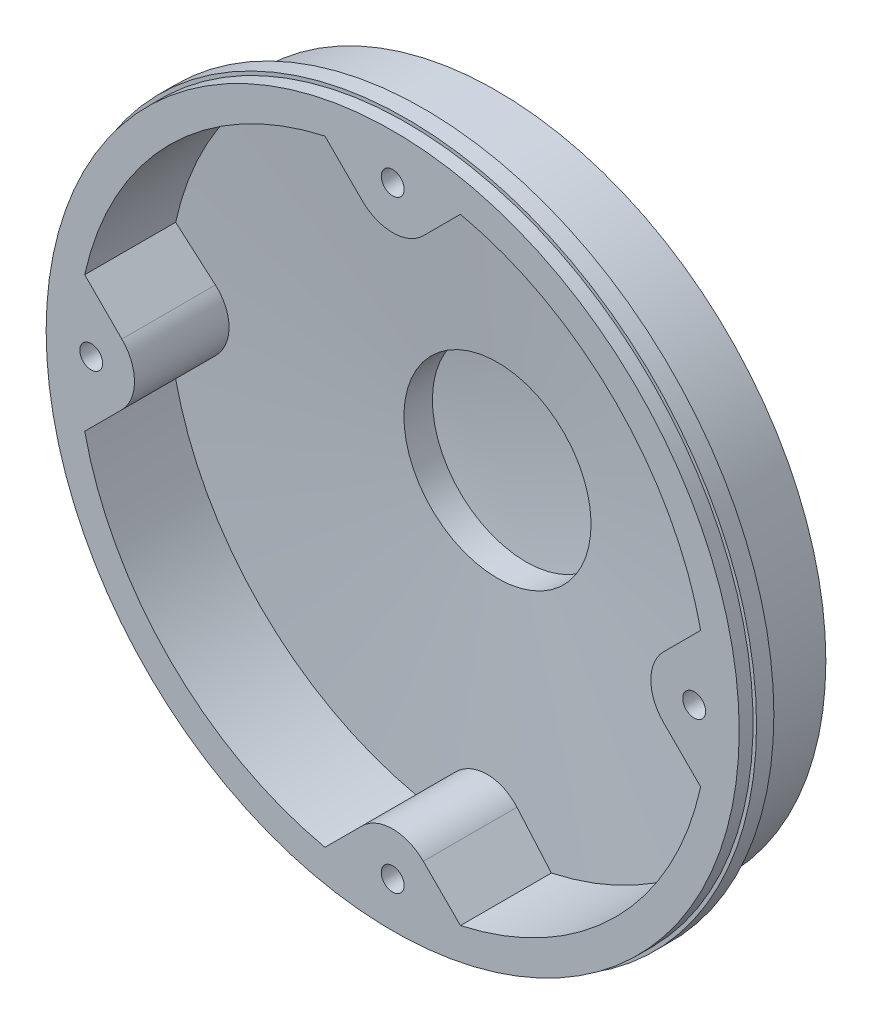
SolidWorks part; units mm, degrees
ref_plane "Front Plane" through (0, 0, 0) normal (0, 0, 1) x (1, 0, 0)
ref_plane "Top Plane" through (0, 0, 0) normal (0, 1, 0) x (1, 0, 0)
ref_plane "Right Plane" through (0, 0, 0) normal (1, 0, 0) x (0, 0, -1)
sketch "Sketch1" plane through (0, 0, 0) normal (0, 0, 1) x (1, 0, 0)
  line L0 (0, 0) -> (55.5, 0) construction
  line L1 (0, 0) -> (-55.5, 0) construction
  line L2 (0, 0) -> (-43.5, 0) construction
  line L3 (0, 0) -> (0, 43.5) construction
  line L4 (0, 0) -> (-53.6089, -14.3645) construction
  line L5 (0, 0) -> (14.3645, 53.6089) construction
  line L6 (0, 0) -> (53.6089, -14.3645) construction
  line L7 (0, -39) -> (-31.5473, -1.4034) construction
  line L8 (0, 0) -> (0, -87.5283) construction
  line L9 (-45.5, -39) -> (45.5, -39) construction
  line L10 (0, -39) -> (-32.7037, -71.7037) construction
  line L11 (0, -39) -> (35.3367, -74.3367) construction
  line L12 (-1.5, -4.0322) -> (-1.5, -21.5644)
  line L13 (1.5, -4.0322) -> (1.5, -21.5644)
  line L14 (25.7867, -15.3347) -> (13.3895, -27.7318)
  line L15 (23.6653, -13.2133) -> (11.2682, -25.6105)
  line L16 (34.9678, -40.5) -> (17.4356, -40.5)
  line L17 (34.9678, -37.5) -> (17.4356, -37.5)
  line L18 (23.6653, -64.7867) -> (11.2682, -52.3895)
  line L19 (25.7867, -62.6653) -> (13.3895, -50.2682)
  line L20 (-1.5, -73.9678) -> (-1.5, -56.4356)
  line L21 (1.5, -73.9678) -> (1.5, -56.4356)
  line L22 (-25.7867, -62.6653) -> (-13.3895, -50.2682)
  line L23 (-23.6653, -64.7867) -> (-11.2682, -52.3895)
  line L24 (-34.9678, -37.5) -> (-17.4356, -37.5)
  line L25 (-34.9678, -40.5) -> (-17.4356, -40.5)
  line L26 (-23.6653, -13.2133) -> (-11.2682, -25.6105)
  line L27 (-25.7867, -15.3347) -> (-13.3895, -27.7318)
  line L28 (0, -39) -> (-8.2523, -16.3271) construction
  line L29 (0, -39) -> (8.2523, -16.3271) construction
  line L30 (0, 0) -> (-39.4042, 22.75) construction
  line L31 (-37.6905, 1.5) -> (-17.4356, 1.5)
  line L32 (-40.1327, 21.4386) -> (-15.8497, 7.4188)
  line L33 (-38.6327, 24.0367) -> (-14.3497, 10.0168)
  line L34 (-24.0367, 38.6327) -> (-10.0168, 14.3497)
  line L35 (-21.4386, 40.1327) -> (-7.4188, 15.8497)
  line L36 (-1.5, 45.4753) -> (-1.5, 17.4356)
  line L37 (1.5, 45.4753) -> (1.5, 17.4356)
  line L38 (21.4386, 40.1327) -> (7.4188, 15.8497)
  line L39 (24.0367, 38.6327) -> (10.0168, 14.3497)
  line L40 (38.6327, 24.0367) -> (14.3497, 10.0168)
  line L41 (40.1327, 21.4386) -> (15.8497, 7.4188)
  line L42 (0, 0) -> (-14.3497, 10.0168) construction
  line L43 (0, 0) -> (-7.4188, 15.8497) construction
  line L44 (37.6905, 1.5) -> (17.4356, 1.5)
  line L45 (0, 0) -> (43.922, 43.922) construction
  line L46 (78.1353, 0.3536) -> (39.2444, 39.2444) construction
  line L47 (0, 0) -> (49.96, 17.6918) construction
  line L48 (49.96, 17.6918) -> (58.0395, 16.9138) construction
  line L49 (58.0395, 16.9138) -> (76.2982, -1.3449) construction
  line L50 (51.7595, 20.0301) -> (59.1726, 19.3163)
  line L51 (59.1726, 19.3163) -> (78.0659, 0.4229)
  line L52 (48.1078, 15.3585) -> (56.9065, 14.5113)
  line L53 (56.9065, 14.5113) -> (74.5304, -3.1126)
  line L54 (78.1353, 0.3536) -> (74.5304, -3.1126)
  line L55 (0.3536, 78.1353) -> (-3.1126, 74.5304)
  line L56 (14.5113, 56.9065) -> (-3.1126, 74.5304)
  line L57 (16.9138, 58.0395) -> (-1.3449, 76.2982) construction
  line L58 (19.3163, 59.1726) -> (0.4229, 78.0659)
  line L59 (20.0301, 51.7595) -> (19.3163, 59.1726)
  line L60 (17.6918, 49.96) -> (16.9138, 58.0395) construction
  line L61 (15.3585, 48.1078) -> (14.5113, 56.9065)
  line L62 (0, 0) -> (-25.25, 43.7343) construction
  line L63 (0, 0) -> (-15.25, 26.4138) construction
  line L64 (0, 0) -> (15.25, 26.4138) construction
  circle A0 centre (0, 0) radius 50.5
  circle A1 centre (0, 0) radius 55.5 construction
  arc A2 (9.9704, 0.7692) -> (-9.9704, 0.7692) centre (0, 0) ccw
  circle A3 centre (0, -39) radius 12.25
  circle A4 centre (0, -39) radius 41
  circle A5 centre (0, -39) radius 20.5 construction
  circle A6 centre (0, -39) radius 17.5
  circle A7 centre (0, -39) radius 35
  circle A8 centre (0, 0) radius 43.5 construction
  circle A9 centre (0, 0) radius 45.5
  circle A10 centre (-43.5, 0) radius 4.5
  circle A11 centre (-43.5, 0) radius 2.25
  circle A12 centre (0, 43.5) radius 4.5
  circle A13 centre (0, 43.5) radius 2.25
  circle A14 centre (43.5, 0) radius 4.5
  circle A15 centre (43.5, 0) radius 2.25
  circle A16 centre (-42.0178, -11.2586) radius 3 construction
  circle A17 centre (-42.0178, -11.2586) radius 6
  circle A18 centre (-42.0178, -11.2586) radius 2.25
  circle A19 centre (11.2586, 42.0178) radius 6
  circle A20 centre (11.2586, 42.0178) radius 3 construction
  circle A21 centre (11.2586, 42.0178) radius 2.25
  circle A22 centre (42.0178, -11.2586) radius 6
  circle A23 centre (42.0178, -11.2586) radius 3 construction
  circle A24 centre (42.0178, -11.2586) radius 2.25
  circle A25 centre (-26.7178, -7.159) radius 2.75
  circle A26 centre (-26.7178, -7.159) radius 4.75
  circle A27 centre (26.7178, -7.159) radius 2.75
  circle A28 centre (26.7178, -7.159) radius 4.75
  circle A29 centre (-29.3449, -68.3449) radius 2.75
  circle A30 centre (-29.3449, -68.3449) radius 4.75
  circle A31 centre (29.3449, -68.3449) radius 2.75
  circle A32 centre (29.3449, -68.3449) radius 4.75
  arc A33 (-3.9292, -21.9468) -> (3.9292, -21.9468) centre (0, -20.2) ccw
  arc A34 (-3.9292, -21.9468) -> (-5.9217, -19.3739) centre (-10.1687, -24.7207) ccw
  arc A35 (3.9292, -21.9468) -> (5.9217, -19.3739) centre (10.1687, -24.7207) cw
  arc A36 (-5.9217, -19.3739) -> (-7.0114, -19.7363) centre (0, -39) ccw
  arc A37 (5.9217, -19.3739) -> (7.0114, -19.7363) centre (0, -39) cw
  arc A38 (8.0792, -20.1592) -> (7.0114, -19.7363) centre (0, -39) ccw
  arc A39 (7.9516, -23.4109) -> (8.0792, -20.1592) centre (1.3889, -21.5251) ccw
  arc A40 (7.9516, -23.4109) -> (13.9715, -28.4621) centre (12.0844, -24.5984) ccw
  arc A41 (13.9715, -28.4621) -> (17.1517, -27.7719) centre (16.9682, -34.5978) cw
  arc A42 (17.1517, -27.7719) -> (17.7535, -28.75) centre (0, -39) cw
  arc A43 (18.2997, -29.7603) -> (17.7535, -28.75) centre (0, -39) ccw
  arc A44 (16.1118, -32.1692) -> (18.2997, -29.7603) centre (12.2966, -26.5062) ccw
  arc A45 (16.1118, -32.1692) -> (17.4764, -39.9083) centre (18.5144, -35.7354) ccw
  arc A46 (17.4764, -39.9083) -> (20.3562, -41.4236) centre (15.8281, -46.5347) cw
  arc A47 (20.3562, -41.4236) -> (20.1886, -42.5598) centre (0, -39) cw
  arc A48 (19.9575, -43.6848) -> (20.1886, -42.5598) centre (0, -39) ccw
  arc A49 (16.7331, -44.1238) -> (19.9575, -43.6848) centre (17.4506, -37.3333) ccw
  arc A50 (16.7331, -44.1238) -> (12.8039, -50.9294) centre (16.2813, -48.4) ccw
  arc A51 (12.8039, -50.9294) -> (14.0359, -53.9414) centre (7.2819, -54.946) cw
  arc A52 (14.0359, -53.9414) -> (13.1771, -54.7039) centre (0, -39) cw
  arc A53 (12.2771, -55.4172) -> (13.1771, -54.7039) centre (0, -39) ccw
  arc A54 (9.5248, -53.6809) -> (12.2771, -55.4172) centre (14.4393, -48.9402) ccw
  arc A55 (9.5248, -53.6809) -> (2.1403, -56.3686) centre (6.43, -56.6662) ccw
  arc A56 (2.1403, -56.3686) -> (1.148, -59.4678) centre (-4.6717, -55.896) cw
  arc A57 (1.148, -59.4678) -> (0, -59.5) centre (0, -39) cw
  arc A58 (-1.148, -59.4678) -> (0, -59.5) centre (0, -39) ccw
  arc A59 (-2.1403, -56.3686) -> (-1.148, -59.4678) centre (4.6717, -55.896) ccw
  arc A60 (-2.1403, -56.3686) -> (-9.5248, -53.6809) centre (-6.43, -56.6662) ccw
  arc A61 (-9.5248, -53.6809) -> (-12.2771, -55.4172) centre (-14.4393, -48.9402) cw
  arc A62 (-12.2771, -55.4172) -> (-13.1771, -54.7039) centre (0, -39) cw
  arc A63 (-14.0359, -53.9414) -> (-13.1771, -54.7039) centre (0, -39) ccw
  arc A64 (-12.8039, -50.9294) -> (-14.0359, -53.9414) centre (-7.2819, -54.946) ccw
  arc A65 (-12.8039, -50.9294) -> (-16.7331, -44.1238) centre (-16.2813, -48.4) ccw
  arc A66 (-16.7331, -44.1238) -> (-19.9575, -43.6848) centre (-17.4506, -37.3333) cw
  arc A67 (-19.9575, -43.6848) -> (-20.1886, -42.5598) centre (0, -39) cw
  arc A68 (-20.3562, -41.4236) -> (-20.1886, -42.5598) centre (0, -39) ccw
  arc A69 (-17.4764, -39.9083) -> (-20.3562, -41.4236) centre (-15.8281, -46.5347) ccw
  arc A70 (-17.4764, -39.9083) -> (-16.1118, -32.1692) centre (-18.5144, -35.7354) ccw
  arc A71 (-16.1118, -32.1692) -> (-18.2997, -29.7603) centre (-12.2966, -26.5062) cw
  arc A72 (-18.2997, -29.7603) -> (-17.7535, -28.75) centre (0, -39) cw
  arc A73 (-17.1517, -27.7719) -> (-17.7535, -28.75) centre (0, -39) ccw
  arc A74 (-13.9715, -28.4621) -> (-17.1517, -27.7719) centre (-16.9682, -34.5978) ccw
  arc A75 (-13.9715, -28.4621) -> (-7.9516, -23.4109) centre (-12.0844, -24.5984) ccw
  arc A76 (-7.9516, -23.4109) -> (-8.0792, -20.1592) centre (-1.3889, -21.5251) cw
  arc A77 (-8.0792, -20.1592) -> (-7.0114, -19.7363) centre (0, -39) cw
  circle A78 centre (0, -39) radius 7
  circle A79 centre (0, -39) radius 6.25
  circle A80 centre (0, -39) radius 4
  circle A81 centre (0, -39) radius 3
  arc A82 (-37.5, 0) -> (-45.1322, 5.7737) centre (-43.5, 0) ccw
  arc A83 (17.3993, -1.875) -> (-17.3993, -1.875) centre (0, 0) ccw
  arc A84 (-5.7737, 45.1322) -> (0, 37.5) centre (0, 43.5) ccw
  circle A85 centre (-15.25, 26.4138) radius 4
  arc A86 (37.5, 0) -> (45.1322, 5.7737) centre (43.5, 0) cw
  arc A87 (37.4767, 37.4767) -> (49.96, 17.6918) centre (0, 0) cw construction
  arc A88 (39.2444, 39.2444) -> (51.7595, 20.0301) centre (0, 0) cw
  arc A89 (35.7089, 35.7089) -> (48.1078, 15.3585) centre (0, 0) cw
  arc A90 (37.4767, 37.4767) -> (17.6918, 49.96) centre (0, 0) ccw construction
  arc A91 (39.2444, 39.2444) -> (20.0301, 51.7595) centre (0, 0) ccw
  circle A92 centre (15.25, 26.4138) radius 4
  circle A93 centre (0, -43.5) radius 2.25
  point P94 (0, -39)
  point P178 (0, -39)
  dimension "D1" = 101
  dimension "D2" = 111
  dimension "D5" = 82
  dimension "D6" = 24.5
  dimension "D7" = 41
  dimension "D8" = 35
  dimension "D9" = 70
  dimension "D10" = 87
  dimension "D12" = 9
  dimension "D13" = 4.5
  dimension "D17" = 6
  dimension "D18" = 12
  dimension "D19" = 4.5
  dimension "D21" = 5.5
  dimension "D22" = 9.5
  dimension "D24" = 5.5
  dimension "D25" = 9.5
  dimension "D29" = 20
  dimension "D30" = 4.3
  dimension "D33" = 14
  dimension "D34" = 12.5
  dimension "D35" = 8
  dimension "D36" = 6
  dimension "D37" = 6
  dimension "D38" = 17.5
  dimension "D39" = 10
  dimension "D40" = 6
  dimension "D49" = 53
  dimension "D54" = 8
  dimension "D4" = 39
  dimension "D15" = 90
  dimension "D16" = 40
  dimension "D20" = 15
  dimension "D23" = 45
  dimension "D26" = 41.5
  dimension "D27" = 1.5
  dimension "D31" = 18.8
  dimension "D41" = 30
  dimension "D42" = 1.5
  dimension "D43" = 1.5
  dimension "D45" = 30
  dimension "D46" = 45
  dimension "D47" = 55
  dimension "D48" = 25.5
  dimension "D50" = 2.5
  dimension "D51" = 25
  dimension "D52" = 60
  dimension "D53" = 20
  dimension "D56" = 60
  dimension "D11" = 5
  dimension "D14" = 3
  dimension "D28" = 8
  dimension "D32" = 9
  dimension "D44" = 5
  dimension "D55" = 2
sketch "Sketch2" plane through (0, 0, 0) normal (0, 0, 1) x (1, 0, 0)
  circle A0 centre (0, 0) radius 50.5 construction
  circle A1 centre (0, 0) radius 50.5
sketch "Sketch12" plane through (0, 0, 0) normal (0, 0, 1) x (1, 0, 0)
  line L0 (0, 0) -> (-55.5, 0) construction
  line L1 (0, 0) -> (55.5, 0) construction
  line L2 (0, 0) -> (0, 43.5) construction
  line L3 (0, 0) -> (0, -87.5283) construction
  line L4 (0, 0) -> (-55.5, 0) construction
  line L5 (0, 0) -> (55.5, 0) construction
  line L6 (0, 0) -> (0, 55.5) construction
  line L7 (0, 0) -> (0, -55.5) construction
  circle A0 centre (0, 43.5) radius 2.25 construction
  circle A1 centre (-43.5, 0) radius 2.25 construction
  circle A2 centre (43.5, 0) radius 2.25 construction
  circle A3 centre (0, -43.5) radius 2.25 construction
  circle A4 centre (0, 0) radius 55.5 construction
  circle A5 centre (0, 0) radius 50.5 construction
  circle A6 centre (0, 43.5) radius 2.25
  circle A7 centre (-43.5, 0) radius 2.25
  circle A8 centre (43.5, 0) radius 2.25
  circle A9 centre (0, -43.5) radius 2.25
  circle A10 centre (0, 0) radius 55.5 construction
  circle A11 centre (0, 0) radius 50.5 construction
sketch "Sketch11" plane through (0, 0, 0) normal (1, 0, 0) x (0, 0, -1)
  line L0 (0, 0) -> (0, 50.5)
  line L1 (0, 0) -> (0, -50.5) construction
  line L2 (0, 0) -> (-74.1731, 0) construction
  line L3 (0, 0) -> (20, 0)
  line L4 (0, 50.5) -> (2.5, 50.5)
  line L5 (0, -50.5) -> (2.5, -50.5) construction
  line L6 (2.5, 50.5) -> (2.5, 47.5)
  line L7 (2.5, -50.5) -> (2.5, -47.5) construction
  line L8 (2.5, 47.5) -> (13, 47.5)
  line L9 (2.5, -47.5) -> (13, -47.5) construction
  line L10 (13, 47.5) -> (15, 15.5)
  line L11 (13, -47.5) -> (15, -15.5) construction
  line L12 (15, 15.5) -> (19, 15.5)
  line L13 (15, -15.5) -> (19, -15.5) construction
  line L14 (15, 15.5) -> (15, 0) construction
  line L15 (15, -15.5) -> (15, 0) construction
  arc A0 (19, 15.5) -> (20, 0) centre (-100.625, 0) cw
  arc A1 (19, -15.5) -> (20, 0) centre (-100.625, 0) ccw construction
  dimension "D2" = 2.5
  dimension "D1" = 101
  dimension "D3" = 10.5
  dimension "D4" = 3
  dimension "D5" = 31
  dimension "D6" = 15
  dimension "D7" = 4
  dimension "D8" = 5
revolve "Revolve1" add sketch "Sketch11" angle 360 about L3
sketch "Sketch13" plane through (0, 0, 0) normal (1, 0, 0) x (0, 0, -1)
  line L0 (2.5, 47.5) -> (13, 47.5) construction
  line L1 (13, 47.5) -> (15, 15.5) construction
  line L2 (15, 15.5) -> (19, 15.5) construction
  line L3 (0, 0) -> (20, 0) construction
  line L4 (0, 50.5) -> (0, -50.5) construction
  line L5 (0, 47.5) -> (13, 47.5) construction
  line L6 (13, 47.5) -> (15, 15.5) construction
  line L7 (15, 15.5) -> (19, 15.5) construction
  line L8 (0, 0) -> (20, 0) construction
  line L9 (0, 47.5) -> (0, -50.5) construction
  line L10 (0, 45.5) -> (11.1211, 45.5)
  line L11 (11.1211, 45.5) -> (13.1211, 13.5)
  line L12 (13.1211, 13.5) -> (17.2293, 13.5)
  line L13 (0, -2) -> (37.8919, -2) construction
  line L14 (-2, 0) -> (-2, 55.9288) construction
  line L15 (0, 0) -> (-74.1731, 0) construction
  line L16 (0, 47.5) -> (13, 47.5) construction
  line L17 (0, 45.5) -> (11.1211, 45.5) construction
  line L18 (0, 45.5) -> (0, 0)
  line L19 (0, 0) -> (18, 0)
  arc A0 (20, 0) -> (19, 15.5) centre (-100.625, 0) ccw construction
  arc A1 (20, 0) -> (19, 15.5) centre (-100.625, 0) ccw construction
  arc A2 (18, 0) -> (17.2293, 13.5) centre (-100.625, 0) ccw
  arc A3 (20, 0) -> (19, 15.5) centre (-100.625, 0) ccw construction
  arc A4 (18, 0) -> (17.2293, 13.5) centre (-100.625, 0) ccw construction
  dimension "D2" = 2
  dimension "D3" = 2
  dimension "D1" = 2
revolve "Cut-Revolve2" cut sketch "Sketch13" angle 360 about L19
sketch "Sketch14" plane through (0, 0, 0) normal (0, 0, 1) x (1, 0, 0)
  line L0 (0, 0) -> (55.5, 0) construction
  line L1 (0, 0) -> (-55.5, 0) construction
  line L2 (0, 0) -> (0, 55.5) construction
  line L3 (0, 0) -> (0, -55.5) construction
  line L4 (0, 0) -> (55.5, 0) construction
  line L5 (0, 0) -> (-55.5, 0) construction
  line L6 (0, 0) -> (0, 55.5) construction
  line L7 (0, 0) -> (0, -55.5) construction
  line L8 (-39.0806, 4.4194) -> (-45.273, 10.6118)
  line L9 (-39.0806, -4.4194) -> (-45.273, -10.6118)
  circle A0 centre (0, 0) radius 45.5 construction
  circle A1 centre (0, 43.5) radius 2.25 construction
  circle A2 centre (-43.5, 0) radius 2.25 construction
  circle A3 centre (0, -43.5) radius 2.25 construction
  circle A4 centre (43.5, 0) radius 2.25 construction
  circle A5 centre (0, 0) radius 45.5 construction
  circle A6 centre (0, 43.5) radius 2.25 construction
  circle A7 centre (-43.5, 0) radius 2.25 construction
  circle A8 centre (0, -43.5) radius 2.25 construction
  circle A9 centre (43.5, 0) radius 2.25 construction
  arc A10 (-45.273, 10.6118) -> (-45.273, -10.6118) centre (0, 0) ccw
  circle A12 centre (0, 0) radius 46.5 construction
  arc A14 (-39.0806, -4.4194) -> (-39.0806, 4.4194) centre (-43.5, 0) ccw
  dimension "D2" = 4
  dimension "D3" = 45
  dimension "D1" = 1
extrude "Boss-Extrude1" add sketch "Sketch14" against normal up to next
pattern_circular "CirPattern1" count 4 over 360 about axis through (0, 0, 0) along (0, 0, 1) of "Boss-Extrude1"
ref_plane "Plane1" through (0, 0, -19) normal (0, 0, 1) x (1, 0, 0)
sketch "Sketch19" plane through (0, 0, -19) normal (0, 0, 1) x (1, 0, 0)
  line L0 (0.5, 15.4919) -> (0.25, 32.4919)
  line L1 (0, 47.5) -> (0, 15.5) construction
  line L2 (0, 15.5) -> (0, 37.5) construction
  line L3 (0, 0) -> (0, 15.5) construction
  line L4 (-0.5, 15.4919) -> (-0.25, 32.4919)
  line L5 (-0.5, 15.4919) -> (0.5, 15.4919)
  circle A0 centre (0, 0) radius 15.5 construction
  arc A1 (0.25, 32.4919) -> (0, 37.5) centre (-71.0371, 31.4436) ccw
  arc A2 (-0.25, 32.4919) -> (0, 37.5) centre (71.0371, 31.4436) cw
  dimension "D1" = 1
  dimension "D2" = 0.5
  dimension "D3" = 37.5
  dimension "D4" = 17
extrude "Boss-Extrude3" add sketch "Sketch19" along normal up to next from offset 1
pattern_circular "CirPattern3" count 16 over 360 about axis through (0, 0, 0) along (0, 0, 1) of "Boss-Extrude3"
sketch "Sketch20" plane through (0, 0, 0) normal (1, 0, 0) x (0, 0, -1)
  line L0 (18, 15.5) -> (13.625, 37.5)
  line L1 (13.625, 37.5) -> (19, 37.5)
  line L2 (19, 55.55) -> (19, -55.55) construction
  line L3 (19, 37.5) -> (19, 15.5)
  line L4 (19, 15.5) -> (18, 15.5)
  line L5 (0, 0) -> (19, 0) construction
  dimension "D1" = 360
  dimension "D2" = 15.5
  dimension "D3" = 1
revolve "Cut-Revolve4" cut sketch "Sketch20" angle 360 about L2
sketch "Sketch10" plane through (0, 0, 0) normal (0, 0, 1) x (1, 0, 0)
  point P0 (-43.5, 0)
  point P1 (0, 43.5)
  point P3 (43.5, 0)
  point P5 (0, -43.5)
hole_wizard "M4x0.7 Tapped Hole1" positions "Sketch16" profile "Sketch15" tap size "M4x0.7" standard "ANSI Metric"
sketch "Sketch16" plane through (0, 0, 0) normal (0, 0, 1) x (1, 0, 0)
  point P0 (-43.5, 0)
  point P3 (0, 43.5)
  point P6 (43.5, 0)
  point P9 (0, -43.5)
sketch "Sketch15" plane through (-43.5, 0, 0) normal (1, 0, 0) x (0, -1, 0)
  line L0 (0, 0) -> (0, 10.9914)
  line L1 (0, 10.9914) -> (1.65, 10)
  line L2 (1.65, 10) -> (1.65, 0)
  line L5 (1.65, 0) -> (0, 0)
  line L10 (0, 10.9914) -> (-1.65, 10) construction
  line L11 (0, -6.35) -> (0, 107.95) construction
  dimension "Tap Drill Dia." = 3.3
  dimension "Tap Drill Depth" = 10
  dimension "Drill Angle" = 118
sketch "Sketch21" plane through (0, 0, 0) normal (0, 0, 1) x (1, 0, 0)
  line L0 (-9.7762, 44.4373) -> (-4.4194, 39.0806) construction
  line L1 (4.4194, 39.0806) -> (9.7762, 44.4373) construction
  line L2 (44.4373, 9.7762) -> (39.0806, 4.4194) construction
  line L3 (39.0806, -4.4194) -> (44.4373, -9.7762) construction
  line L4 (9.7762, -44.4373) -> (4.4194, -39.0806) construction
  line L5 (-4.4194, -39.0806) -> (-9.7762, -44.4373) construction
  line L6 (-9.7762, 44.4373) -> (-4.4194, 39.0806)
  line L7 (4.4194, 39.0806) -> (9.7762, 44.4373)
  line L8 (44.4373, 9.7762) -> (39.0806, 4.4194)
  line L9 (39.0806, -4.4194) -> (44.4373, -9.7762)
  line L10 (9.7762, -44.4373) -> (4.4194, -39.0806)
  line L11 (-4.4194, -39.0806) -> (-9.7762, -44.4373)
  line L12 (-44.4373, -9.7762) -> (-39.0806, -4.4194) construction
  line L13 (-39.0806, 4.4194) -> (-44.4373, 9.7762) construction
  line L14 (-44.4373, -9.7762) -> (-39.0806, -4.4194)
  line L15 (-39.0806, 4.4194) -> (-44.4373, 9.7762)
  circle A1 centre (0, 0) radius 50
  circle A2 centre (0, 0) radius 50.5 construction
  arc A3 (-4.4194, 39.0806) -> (4.4194, 39.0806) centre (0, 43.5) ccw construction
  circle A4 centre (0, 43.5) radius 1.65
  circle A5 centre (0, 43.5) radius 1.65
  circle A6 centre (-43.5, 0) radius 1.65
  circle A7 centre (-43.5, 0) radius 1.65
  circle A8 centre (43.5, 0) radius 1.65
  circle A9 centre (43.5, 0) radius 1.65
  circle A10 centre (0, -43.5) radius 1.65
  circle A11 centre (0, -43.5) radius 1.65
  arc A12 (44.4373, 9.7762) -> (9.7762, 44.4373) centre (0, 0) ccw construction
  arc A13 (39.0806, 4.4194) -> (39.0806, -4.4194) centre (43.5, 0) ccw construction
  arc A14 (9.7762, -44.4373) -> (44.4373, -9.7762) centre (0, 0) ccw construction
  arc A15 (4.4194, -39.0806) -> (-4.4194, -39.0806) centre (0, -43.5) ccw construction
  arc A16 (-44.4373, -9.7762) -> (-9.7762, -44.4373) centre (0, 0) ccw construction
  arc A17 (-4.4194, 39.0806) -> (4.4194, 39.0806) centre (0, 43.5) ccw
  arc A18 (44.4373, 9.7762) -> (9.7762, 44.4373) centre (0, 0) ccw
  arc A19 (39.0806, 4.4194) -> (39.0806, -4.4194) centre (43.5, 0) ccw
  arc A20 (9.7762, -44.4373) -> (44.4373, -9.7762) centre (0, 0) ccw
  arc A21 (4.4194, -39.0806) -> (-4.4194, -39.0806) centre (0, -43.5) ccw
  arc A22 (-44.4373, -9.7762) -> (-9.7762, -44.4373) centre (0, 0) ccw
  arc A23 (-39.0806, -4.4194) -> (-39.0806, 4.4194) centre (-43.5, 0) ccw construction
  arc A24 (-9.7762, 44.4373) -> (-44.4373, 9.7762) centre (0, 0) ccw construction
  arc A25 (-39.0806, -4.4194) -> (-39.0806, 4.4194) centre (-43.5, 0) ccw
  arc A26 (-9.7762, 44.4373) -> (-44.4373, 9.7762) centre (0, 0) ccw
  dimension "D1" = 0.5
  dimension "D2" = 0
  dimension "D3" = 0
  dimension "D4" = 0
  dimension "D5" = 0
extrude "Boss-Extrude4" add sketch "Sketch21" along normal blind 2
